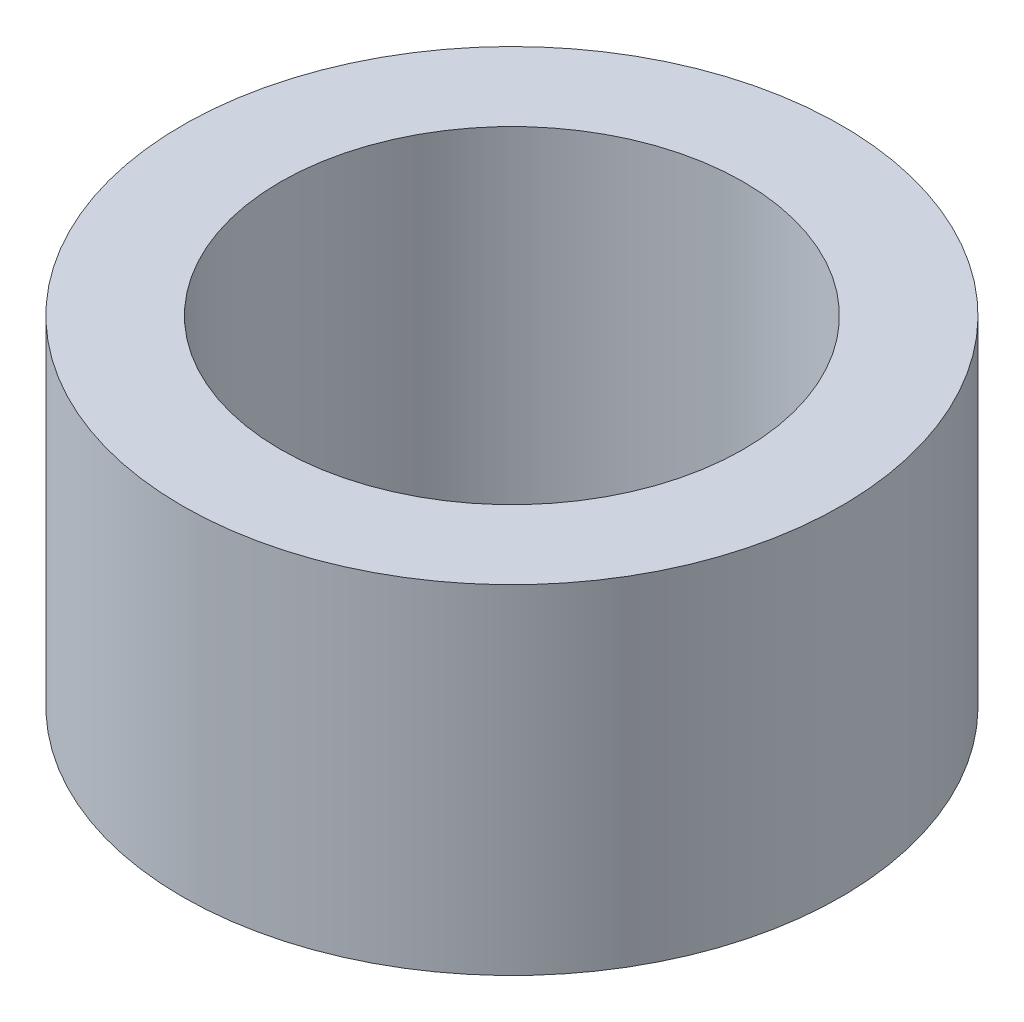
SolidWorks part; units mm, degrees
ref_plane "Front Plane" through (0, 0, 0) normal (0, 0, 1) x (1, 0, 0)
ref_plane "Top Plane" through (0, 0, 0) normal (0, 1, 0) x (1, 0, 0)
ref_plane "Right Plane" through (0, 0, 0) normal (1, 0, 0) x (0, 0, -1)
sketch "Sketch1" plane through (0, 0, 0) normal (0, 1, 0) x (1, 0, 0)
  circle A0 centre (0, 0) radius 4.699
  circle A1 centre (0, 0) radius 3.302
  dimension "D1" = 6.604
  dimension "D2" = 9.398
extrude "Boss-Extrude1" add sketch "Sketch1" along normal blind 4.826
